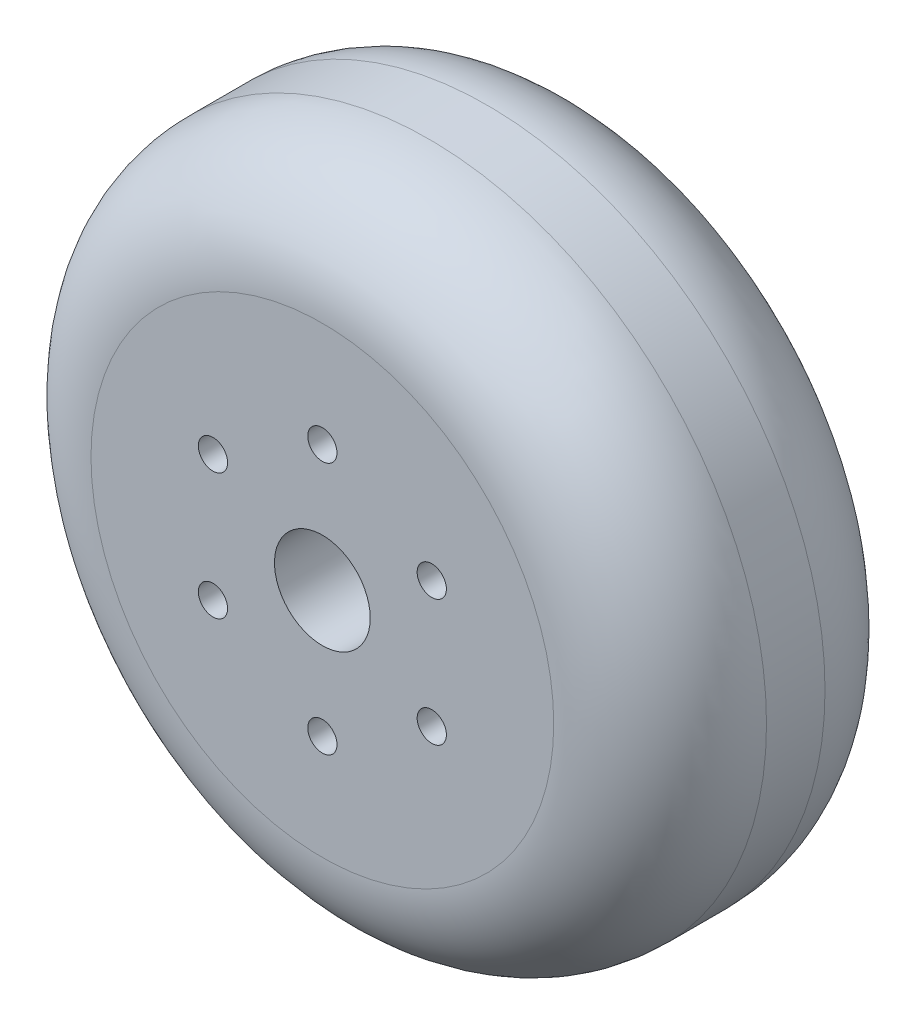
SolidWorks part; units mm, degrees
ref_plane "Front Plane" through (0, 0, 0) normal (0, 0, 1) x (1, 0, 0)
ref_plane "Top Plane" through (0, 0, 0) normal (0, 1, 0) x (1, 0, 0)
ref_plane "Right Plane" through (0, 0, 0) normal (1, 0, 0) x (0, 0, -1)
sketch "Sketch1" plane through (0, 0, 0) normal (0, 0, 1) x (1, 0, 0)
  circle A0 centre (0, 0) radius 63.5
  circle A1 centre (0, 0) radius 9
  dimension "D1" = 127
  dimension "D2" = 18
extrude "Boss-Extrude1" add sketch "Sketch1" along normal blind 51
fillet "Fillet1" radius 20 2 edges at (63.5, 0, 0) (63.5, 0, 51)
hole_wizard "M5 Clearance Hole1" positions "Sketch2" profile "Sketch3" hole size "M5" standard "DIN" end condition through all
sketch "Sketch2" plane through (0, 0, 51) normal (0, 0, 1) x (1, 0, 0)
  point P0 (0, 23.75)
  point P11 (20.5681, 11.875)
  point P12 (20.5681, -11.875)
  point P13 (0, -23.75)
  point P14 (-20.5681, -11.875)
  point P15 (-20.5681, 11.875)
  point P19 (0, 0)
  dimension "D1" = 23.75
  dimension "D2" = 6
sketch "Sketch3" plane through (0, 23.75, 51) normal (1, 0, 0) x (0, -1, 0)
  line L0 (0, 0) -> (0, 51)
  line L1 (0, 51) -> (2.75, 51)
  line L2 (2.75, 51) -> (2.75, 0)
  line L5 (2.75, 0) -> (0, 0)
  line L11 (0, -6.35) -> (0, 107.95) construction
  dimension "Thru Hole Dia." = 5.5
  dimension "Thru Hole Depth" = 51
